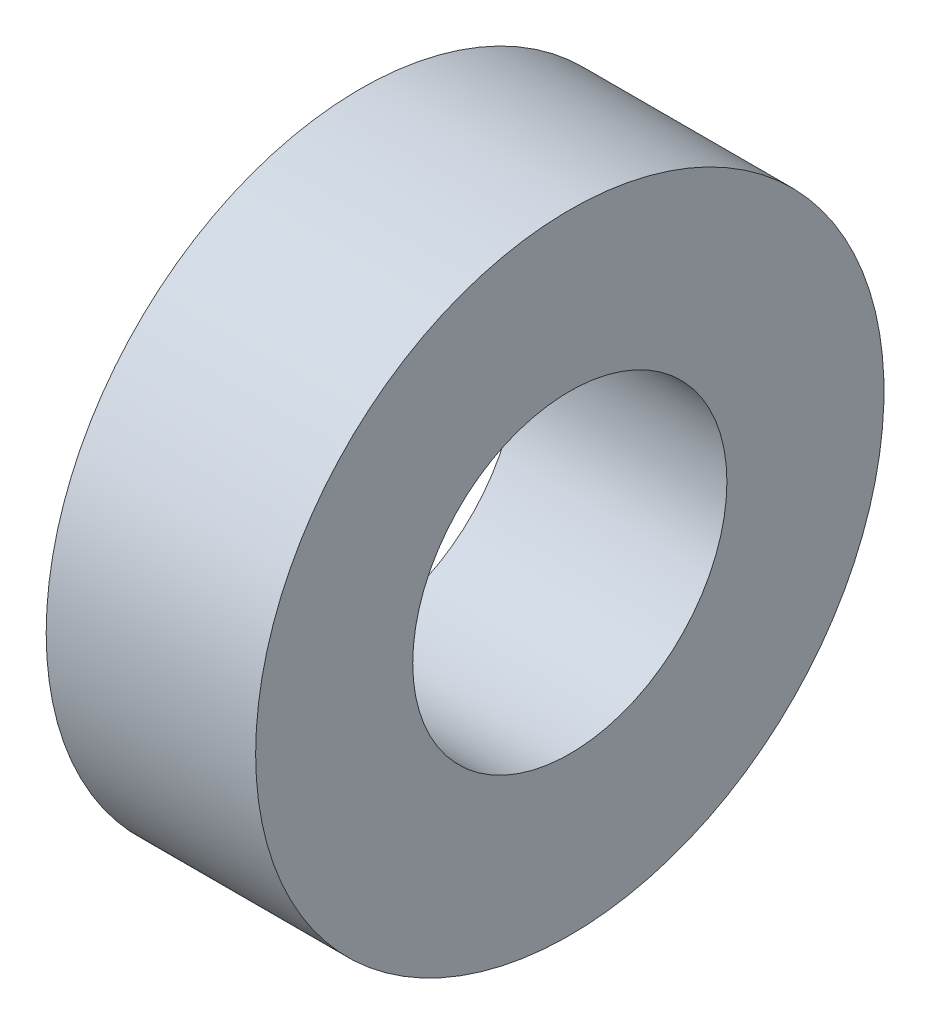
SolidWorks part; units mm, degrees
ref_plane "Front Plane" through (0, 0, 0) normal (0, 0, 1) x (1, 0, 0)
ref_plane "Top Plane" through (0, 0, 0) normal (0, 1, 0) x (1, 0, 0)
ref_plane "Right Plane" through (0, 0, 0) normal (1, 0, 0) x (0, 0, -1)
sketch "Sketch3" plane through (0, 0, 0) normal (0, 0, 1) x (1, 0, 0)
  line L0 (0, 0) -> (4.9032, 0) construction
  line L1 (0, 1.5) -> (0, 3)
  line L2 (0, 3) -> (2, 3)
  line L3 (2, 3) -> (2, 1.5)
  line L4 (2, 1.5) -> (0, 1.5)
  dimension "D1" = 1.5
  dimension "D2" = 2
  dimension "D3" = 3
revolve "Revolve1" add sketch "Sketch3" angle 360 about L0
